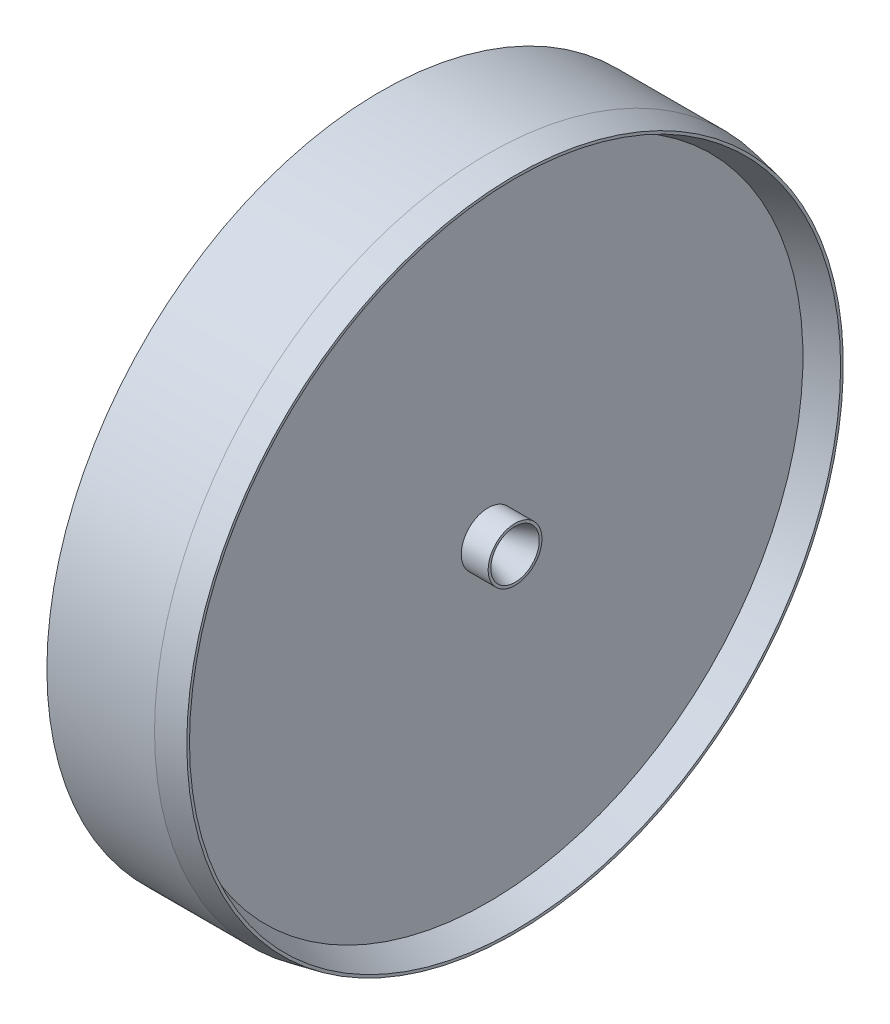
SolidWorks part; units mm, degrees
ref_plane "Płaszczyzna przednia" through (0, 0, 0) normal (0, 0, 1) x (1, 0, 0)
ref_plane "Płaszczyzna górna" through (0, 0, 0) normal (0, 1, 0) x (1, 0, 0)
ref_plane "Płaszczyzna prawa" through (0, 0, 0) normal (1, 0, 0) x (0, 0, -1)
sketch "Szkic1" plane through (0, 0, 0) normal (0, 0, 1) x (1, 0, 0)
  line L0 (0, 12.4) -> (0, 0)
  line L1 (0, 0) -> (4, 0)
  line L2 (4, 0) -> (4, 0.5)
  line L3 (4, 0.5) -> (5, 0.9)
  line L4 (5, 0.9) -> (5, 1)
  line L5 (5, 1) -> (4, 1)
  line L6 (4, 1) -> (4, 11.7)
  line L7 (4, 11.7) -> (5, 12.1)
  line L8 (5, 12.1) -> (5, 12.2)
  line L9 (5, 12.2) -> (4, 12.4)
  line L10 (4, 12.4) -> (0, 12.4)
  dimension "D1" = 12.4
  dimension "D2" = 4
  dimension "D3" = 1
  dimension "D4" = 0.1
  dimension "D5" = 12.2
  dimension "D6" = 1
  dimension "D7" = 0.5
revolve "Obrót1" add sketch "Szkic1" angle 360 about L1
